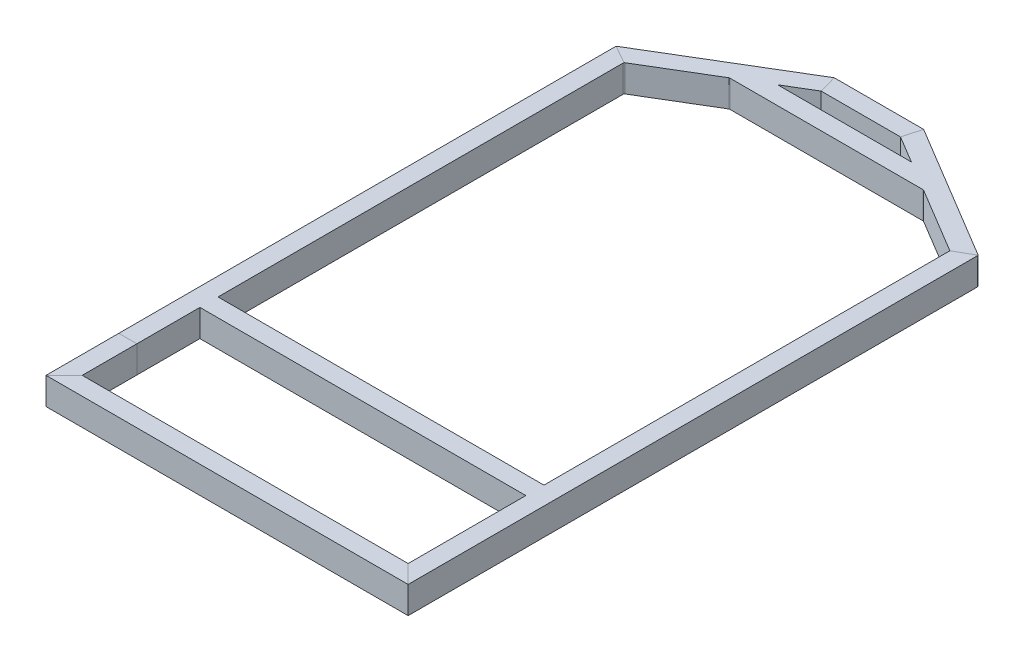
SolidWorks part; units mm, degrees
material "6061-T6 (SS)"
ref_plane "Front Plane" through (0, 0, 0) normal (0, 0, 1) x (1, 0, 0)
ref_plane "Top Plane" through (0, 0, 0) normal (0, 1, 0) x (1, 0, 0)
ref_plane "Right Plane" through (0, 0, 0) normal (1, 0, 0) x (0, 0, -1)
sketch "Sketch2" plane through (0, 0, 0) normal (0, 0, 1) x (1, 0, 0)
  line L0 (2.9718, 2.9718) -> (2.9718, 72.9488)
  line L1 (0, 0) -> (50.8, 0)
  line L2 (0, 0) -> (0, 75.9206)
  line L3 (0, 75.9206) -> (50.8, 75.9206)
  line L4 (50.8, 0) -> (50.8, 75.9206)
  line L5 (2.9718, 72.9488) -> (47.8282, 72.9488)
  line L6 (47.8282, 2.9718) -> (47.8282, 72.9488)
  line L7 (2.9718, 2.9718) -> (47.8282, 2.9718)
  dimension "D1" = 50.8
  dimension "D2" = 75.9206
  dimension "D3" = 2.9718
sketch "Sketch3" plane through (0, 0, 0) normal (0, 1, 0) x (1, 0, 0)
  line L0 (0, -204.2007) -> (0, 1395.2069)
  line L1 (0, 1395.2069) -> (382.5875, 1624.5993)
  line L2 (382.5875, 1624.5993) -> (633.4125, 1624.5993)
  line L3 (633.4125, 1624.5993) -> (1016, 1395.2069)
  line L4 (1016, 1395.2069) -> (1016, -204.2007)
  line L5 (1016, -204.2007) -> (0, -204.2007)
  point P3 (508, 1624.5993)
  point P7 (508, -204.2007)
  dimension "D1" = 1016
  dimension "D2" = 250.825
  dimension "D3" = 446.0875
  dimension "D4" = 446.0875
  dimension "D5" = 1828.8
sweep "Sweep1" add profiles "Sketch2" path "Sketch3"
sketch "Sketch4" plane through (0, 0, 0) normal (0, -1, 0) x (1, 0, 0)
  line L0 (469.9508, 178.8007) -> (546.0492, 178.8007) construction
  line L2 (469.9508, 188.313) -> (546.0492, 188.313)
  line L3 (469.9508, 169.2884) -> (546.0492, 169.2884)
  line L15 (0, 204.2007) -> (1016, 204.2007) construction
  line L16 (0, 0) -> (0, 204.2007) construction
  arc A0 (469.9508, 188.313) -> (469.9508, 169.2884) centre (469.9508, 178.8007) ccw
  arc A1 (546.0492, 169.2884) -> (546.0492, 188.313) centre (546.0492, 178.8007) ccw
  point P4 (508, 178.8007)
  point P9 (460.4385, 178.8007)
  point P10 (555.5615, 178.8007)
  dimension "D1" = 19.0246
  dimension "D2" = 95.123
  dimension "D3" = 25.4
  dimension "D7" = 508
extrude "Cut-Extrude1" cut sketch "Sketch4" against normal blind 25.4 contours L2 A1 L3 A0
sketch "Sketch5" plane through (0, 0, 0) normal (0, -1, 0) x (1, 0, 0)
  line L0 (469.9, -1599.1993) -> (546.1, -1599.1993) construction
  line L1 (469.9, -1589.687) -> (546.1, -1589.687)
  line L2 (469.9, -1608.7116) -> (546.1, -1608.7116)
  line L3 (633.4125, -1624.5993) -> (382.5875, -1624.5993) construction
  line L4 (469.9508, 188.313) -> (546.0492, 188.313) construction
  line L6 (508, 188.313) -> (508, -2102.7934) construction
  arc A0 (469.9, -1589.687) -> (469.9, -1608.7116) centre (469.9, -1599.1993) ccw
  arc A1 (546.1, -1608.7116) -> (546.1, -1589.687) centre (546.1, -1599.1993) ccw
  point P2 (508, -1599.1993)
  point P13 (460.3877, -1599.1993)
  point P14 (555.6123, -1599.1993)
  dimension "D1" = 95.2246
  dimension "D2" = 19.0246
  dimension "D3" = 25.4
extrude "Cut-Extrude2" cut sketch "Sketch5" against normal blind 25.4
sketch "Sketch7" plane through (965.2, 0, 0) normal (-1, 0, 0) x (0, 0, 1)
  line L0 (-227.1675, 0.4318) -> (-227.1675, 75.4888)
  line L1 (-227.5993, 0) -> (-176.7993, 0)
  line L2 (-227.5993, 0) -> (-227.5993, 75.9206)
  line L3 (-227.5993, 75.9206) -> (-176.7993, 75.9206)
  line L4 (-176.7993, 0) -> (-176.7993, 75.9206)
  line L5 (-227.1675, 75.4888) -> (-177.2311, 75.4888)
  line L6 (-177.2311, 0.4318) -> (-177.2311, 75.4888)
  line L7 (-227.1675, 0.4318) -> (-177.2311, 0.4318)
  line L10 (153.4007, 0) -> (-1366.4341, 0) construction
  line L11 (153.4007, 75.9206) -> (153.4007, 0) construction
  dimension "D1" = 50.8
  dimension "D2" = 75.9206
  dimension "D3" = 0.4318
  dimension "D4" = 0.4318
  dimension "D5" = 330.2
  dimension "D6" = 0.4318
  dimension "D7" = 0.4318
extrude "Boss-Extrude1" add sketch "Sketch7" along normal up to next contours L4 L3 L2 L1
sketch "Sketch8" plane through (0, 0, 0) normal (0, -1, 0) x (1, 0, 0)
  line L0 (469.9508, -202.1993) -> (546.0492, -202.1993) construction
  line L1 (469.9508, -192.687) -> (546.0492, -192.687)
  line L2 (469.9508, -211.7116) -> (546.0492, -211.7116)
  line L3 (0, -1395.2069) -> (0, 0) construction
  line L4 (50.8, -176.7993) -> (965.2, -176.7993) construction
  arc A0 (469.9508, -192.687) -> (469.9508, -211.7116) centre (469.9508, -202.1993) ccw
  arc A1 (546.0492, -211.7116) -> (546.0492, -192.687) centre (546.0492, -202.1993) ccw
  point P2 (508, -202.1993)
  point P13 (555.5615, -202.1993)
  point P14 (460.4385, -202.1993)
  dimension "D1" = 508
  dimension "D2" = 25.4
  dimension "D3" = 19.0246
  dimension "D4" = 95.123
extrude "Cut-Extrude3" cut sketch "Sketch8" against normal blind 25.4
ref_plane "Plane1" through (508, 0, 0) normal (1, 0, 0) x (0, 0, -1)
sketch "Sketch11" plane through (508, 0, 0) normal (1, 0, 0) x (0, 0, -1)
  line L0 (-201.2289, 2.9718) -> (1393.5237, 2.9718) construction
  line L1 (179.7711, 2.9718) -> (224.6275, 2.9718)
  line L2 (179.7711, 2.9718) -> (179.7711, 72.9488)
  line L3 (179.7711, 72.9488) -> (224.6275, 72.9488)
  line L4 (224.6275, 2.9718) -> (224.6275, 72.9488)
  line L5 (-201.2289, 72.9488) -> (1393.5237, 72.9488) construction
  line L7 (227.5993, 0) -> (227.5993, 75.9206) construction
  line L8 (176.7993, 0) -> (176.7993, 75.9206) construction
  dimension "D1" = 2.9718
  dimension "D2" = 2.9718
extrude "Cut-Extrude4" cut sketch "Sketch11" against normal blind 482.6 and the other way blind 482.6
sketch "Sketch12" plane through (0, 0, 0) normal (0, 1, 0) x (1, 0, 0)
  line L0 (320.3967, 1528.0793) -> (695.6033, 1528.0793)
  line L1 (396.6499, 1573.7993) -> (50.8, 1366.4341) construction
  line L2 (965.2, 1366.4341) -> (619.3501, 1573.7993) construction
  line L3 (695.6033, 1528.0793) -> (780.3291, 1477.2793)
  line L4 (780.3291, 1477.2793) -> (235.6709, 1477.2793)
  line L5 (235.6709, 1477.2793) -> (320.3967, 1528.0793)
  line L7 (619.3501, 1573.7993) -> (396.6499, 1573.7993) construction
  dimension "D1" = 50.8
  dimension "D2" = 45.72
extrude "Boss-Extrude2" add sketch "Sketch12" along normal blind 75.9206
sketch "Sketch13" plane through (508, 0, 0) normal (1, 0, 0) x (0, 0, -1)
  line L0 (1480.2511, 2.9718) -> (1525.1075, 2.9718)
  line L1 (1480.2511, 2.9718) -> (1480.2511, 72.9488)
  line L2 (1480.2511, 72.9488) -> (1525.1075, 72.9488)
  line L3 (1525.1075, 2.9718) -> (1525.1075, 72.9488)
  line L4 (1393.5237, 2.9718) -> (1621.6275, 2.9718) construction
  line L5 (1393.5237, 72.9488) -> (1621.6275, 72.9488) construction
  line L6 (1477.2793, 75.9206) -> (1477.2793, 0) construction
  line L7 (1528.0793, 75.9206) -> (1528.0793, 0) construction
  dimension "D1" = 2.9718
  dimension "D2" = 2.9718
extrude "Cut-Extrude5" cut sketch "Sketch13" against normal blind 279.4 and the other way blind 279.4
sketch "Sketch14" plane through (0, 0, 0) normal (0, -1, 0) x (1, 0, 0)
  line L0 (469.9508, -1502.6793) -> (546.0492, -1502.6793) construction
  line L1 (469.9508, -1493.167) -> (546.0492, -1493.167)
  line L2 (469.9508, -1512.1916) -> (546.0492, -1512.1916)
  line L3 (695.6033, -1528.0793) -> (320.3967, -1528.0793) construction
  line L5 (508, -41.7563) -> (508, 41.7563) construction
  arc A0 (469.9508, -1493.167) -> (469.9508, -1512.1916) centre (469.9508, -1502.6793) ccw
  arc A1 (546.0492, -1512.1916) -> (546.0492, -1493.167) centre (546.0492, -1502.6793) ccw
  point P2 (508, -1502.6793)
  point P13 (460.4385, -1502.6793)
  point P14 (555.5615, -1502.6793)
  dimension "D1" = 95.123
  dimension "D2" = 19.0246
  dimension "D3" = 25.4
extrude "Cut-Extrude6" cut sketch "Sketch14" against normal blind 25.4
fillet "Fillet2" radius 4.191 4 edges at (0, 37.9603, -1395.2069) (382.5875, 37.9603, -1624.5993) (633.4125, 37.9603, -1624.5993) (1016, 37.9603, -1395.2069)
fillet "Fillet3" radius 4.191 4 edges at (968.1718, 37.9603, -1368.1174) (780.3291, 37.9603, -1477.2793) (235.6709, 37.9603, -1477.2793) (50.8, 37.9603, -1366.4341)
